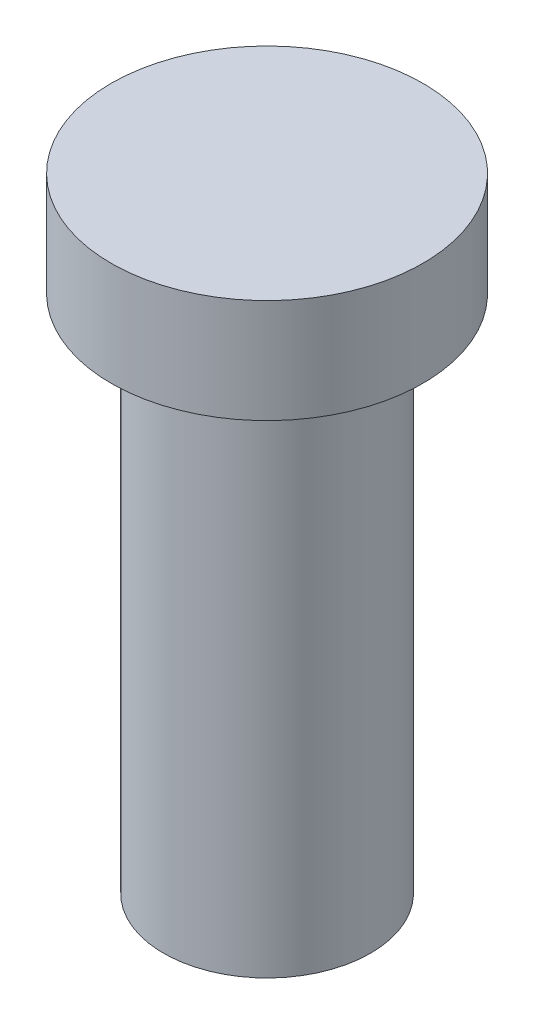
SolidWorks part; units mm, degrees
material "ABS"
ref_plane "Front Plane" through (0, 0, 0) normal (0, 0, 1) x (1, 0, 0)
ref_plane "Top Plane" through (0, 0, 0) normal (0, 1, 0) x (1, 0, 0)
ref_plane "Right Plane" through (0, 0, 0) normal (1, 0, 0) x (0, 0, -1)
sketch "Sketch1" plane through (0, 0, 0) normal (0, 0, 1) x (1, 0, 0)
  line L0 (0, 0) -> (6.3246, 0)
  line L3 (6.3246, 0) -> (6.3246, 31.75)
  line L4 (6.3246, 31.75) -> (9.525, 31.75)
  line L5 (9.525, 31.75) -> (9.525, 38.1)
  line L6 (9.525, 38.1) -> (0, 38.1)
  line L7 (0, 38.1) -> (0, 0)
  dimension "D2" = 6.35
  dimension "D3" = 9.525
  dimension "D4" = 6.3246
  dimension "D5" = 38.1
revolve "Revolve1" add sketch "Sketch1" angle 360 about L7
